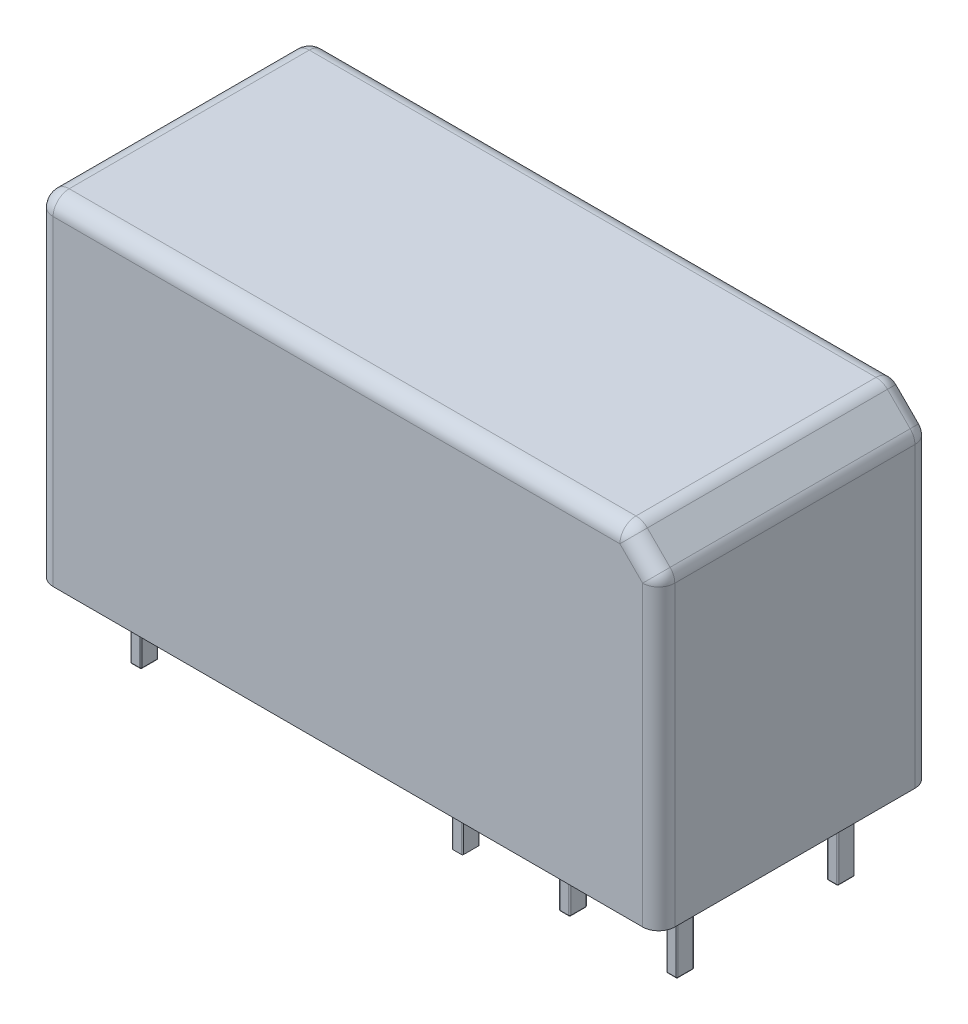
SolidWorks part; units mm, degrees
ref_plane "Спереди" through (0, 0, 0) normal (0, 0, 1) x (1, 0, 0)
ref_plane "Сверху" through (0, 0, 0) normal (0, 1, 0) x (1, 0, 0)
ref_plane "Справа" through (0, 0, 0) normal (1, 0, 0) x (0, 0, -1)
sketch "Эскиз1" plane through (0, 0, 0) normal (0, 1, 0) x (1, 0, 0)
  line L1 (-14.5, -6.35) -> (14.5, -6.35)
  line L2 (-14.5, -6.35) -> (-14.5, 6.35)
  line L3 (-14.5, 6.35) -> (14.5, 6.35)
  line L4 (14.5, -6.35) -> (14.5, 6.35)
  line L5 (-14.5, -6.35) -> (14.5, 6.35) construction
  line L6 (-14.5, 6.35) -> (14.5, -6.35) construction
  point P0 (0, 0)
  dimension "D1" = 29
  dimension "D2" = 12.7
extrude "Бобышка-Вытянуть1" add sketch "Эскиз1" along normal blind 15.7
sketch "Эскиз2" plane through (0, 0, 0) normal (0, -1, 0) x (1, 0, 0)
  line L0 (-14.5, -6.35) -> (-14.5, 6.35) construction
  line L1 (-12.3, 4.15) -> (-11.9, 4.15)
  line L2 (-12.35, 4.1) -> (-12.35, 3.4)
  line L3 (-12.3, 3.35) -> (-11.9, 3.35)
  line L4 (-11.85, 4.1) -> (-11.85, 3.4)
  line L5 (-12.35, 4.15) -> (-11.85, 3.35) construction
  line L6 (-12.35, 3.35) -> (-11.85, 4.15) construction
  line L7 (-7.35, 4.1) -> (-7.35, 3.4) [skipped]
  line L8 (-6.85, 4.1) -> (-6.85, 3.4) [skipped]
  line L9 (-7.3, 4.15) -> (-6.9, 4.15) [skipped]
  line L10 (-7.3, 3.35) -> (-6.9, 3.35) [skipped]
  line L11 (-2.35, 4.1) -> (-2.35, 3.4) [skipped]
  line L12 (-1.85, 4.1) -> (-1.85, 3.4) [skipped]
  line L13 (-2.3, 4.15) -> (-1.9, 4.15) [skipped]
  line L14 (-2.3, 3.35) -> (-1.9, 3.35) [skipped]
  line L15 (2.65, 4.1) -> (2.65, 3.4)
  line L16 (3.15, 4.1) -> (3.15, 3.4)
  line L17 (2.7, 4.15) -> (3.1, 4.15)
  line L18 (2.7, 3.35) -> (3.1, 3.35)
  line L19 (7.65, 4.1) -> (7.65, 3.4)
  line L20 (8.15, 4.1) -> (8.15, 3.4)
  line L21 (7.7, 4.15) -> (8.1, 4.15)
  line L22 (7.7, 3.35) -> (8.1, 3.35)
  line L23 (12.65, 4.1) -> (12.65, 3.4)
  line L24 (13.15, 4.1) -> (13.15, 3.4)
  line L25 (12.7, 4.15) -> (13.1, 4.15)
  line L26 (12.7, 3.35) -> (13.1, 3.35)
  line L27 (-7.35, -3.4) -> (-7.35, -4.1) [skipped]
  line L28 (-6.85, -3.4) -> (-6.85, -4.1) [skipped]
  line L29 (-7.3, -3.35) -> (-6.9, -3.35) [skipped]
  line L30 (-7.3, -4.15) -> (-6.9, -4.15) [skipped]
  line L31 (-2.35, -3.4) -> (-2.35, -4.1) [skipped]
  line L32 (-1.85, -3.4) -> (-1.85, -4.1) [skipped]
  line L33 (-2.3, -3.35) -> (-1.9, -3.35) [skipped]
  line L34 (-2.3, -4.15) -> (-1.9, -4.15) [skipped]
  line L35 (2.65, -3.4) -> (2.65, -4.1)
  line L36 (3.15, -3.4) -> (3.15, -4.1)
  line L37 (2.7, -3.35) -> (3.1, -3.35)
  line L38 (2.7, -4.15) -> (3.1, -4.15)
  line L39 (7.65, -3.4) -> (7.65, -4.1)
  line L40 (8.15, -3.4) -> (8.15, -4.1)
  line L41 (7.7, -3.35) -> (8.1, -3.35)
  line L42 (7.7, -4.15) -> (8.1, -4.15)
  line L43 (12.65, -3.4) -> (12.65, -4.1)
  line L44 (13.15, -3.4) -> (13.15, -4.1)
  line L45 (12.7, -3.35) -> (13.1, -3.35)
  line L46 (12.7, -4.15) -> (13.1, -4.15)
  line L47 (-12.35, -3.4) -> (-12.35, -4.1)
  line L48 (-11.85, -3.4) -> (-11.85, -4.1)
  line L49 (-12.3, -3.35) -> (-11.9, -3.35)
  line L50 (-12.3, -4.15) -> (-11.9, -4.15)
  arc A0 (-12.35, 3.4) -> (-12.3, 3.35) centre (-12.3, 3.4) ccw
  arc A1 (-11.9, 3.35) -> (-11.85, 3.4) centre (-11.9, 3.4) ccw
  arc A2 (-11.9, 4.15) -> (-11.85, 4.1) centre (-11.9, 4.1) cw
  arc A3 (-12.3, 4.15) -> (-12.35, 4.1) centre (-12.3, 4.1) ccw
  arc A4 (-7.35, 3.4) -> (-7.3, 3.35) centre (-7.3, 3.4) ccw [skipped]
  arc A5 (-6.9, 3.35) -> (-6.85, 3.4) centre (-6.9, 3.4) ccw [skipped]
  arc A6 (-6.9, 4.15) -> (-6.85, 4.1) centre (-6.9, 4.1) cw [skipped]
  arc A7 (-7.3, 4.15) -> (-7.35, 4.1) centre (-7.3, 4.1) ccw [skipped]
  arc A8 (-2.35, 3.4) -> (-2.3, 3.35) centre (-2.3, 3.4) ccw [skipped]
  arc A9 (-1.9, 3.35) -> (-1.85, 3.4) centre (-1.9, 3.4) ccw [skipped]
  arc A10 (-1.9, 4.15) -> (-1.85, 4.1) centre (-1.9, 4.1) cw [skipped]
  arc A11 (-2.3, 4.15) -> (-2.35, 4.1) centre (-2.3, 4.1) ccw [skipped]
  arc A12 (2.65, 3.4) -> (2.7, 3.35) centre (2.7, 3.4) ccw
  arc A13 (3.1, 3.35) -> (3.15, 3.4) centre (3.1, 3.4) ccw
  arc A14 (3.1, 4.15) -> (3.15, 4.1) centre (3.1, 4.1) cw
  arc A15 (2.7, 4.15) -> (2.65, 4.1) centre (2.7, 4.1) ccw
  arc A16 (7.65, 3.4) -> (7.7, 3.35) centre (7.7, 3.4) ccw
  arc A17 (8.1, 3.35) -> (8.15, 3.4) centre (8.1, 3.4) ccw
  arc A18 (8.1, 4.15) -> (8.15, 4.1) centre (8.1, 4.1) cw
  arc A19 (7.7, 4.15) -> (7.65, 4.1) centre (7.7, 4.1) ccw
  arc A20 (12.65, 3.4) -> (12.7, 3.35) centre (12.7, 3.4) ccw
  arc A21 (13.1, 3.35) -> (13.15, 3.4) centre (13.1, 3.4) ccw
  arc A22 (13.1, 4.15) -> (13.15, 4.1) centre (13.1, 4.1) cw
  arc A23 (12.7, 4.15) -> (12.65, 4.1) centre (12.7, 4.1) ccw
  arc A24 (-7.35, -4.1) -> (-7.3, -4.15) centre (-7.3, -4.1) ccw [skipped]
  arc A25 (-6.9, -4.15) -> (-6.85, -4.1) centre (-6.9, -4.1) ccw [skipped]
  arc A26 (-6.9, -3.35) -> (-6.85, -3.4) centre (-6.9, -3.4) cw [skipped]
  arc A27 (-7.3, -3.35) -> (-7.35, -3.4) centre (-7.3, -3.4) ccw [skipped]
  arc A28 (-2.35, -4.1) -> (-2.3, -4.15) centre (-2.3, -4.1) ccw [skipped]
  arc A29 (-1.9, -4.15) -> (-1.85, -4.1) centre (-1.9, -4.1) ccw [skipped]
  arc A30 (-1.9, -3.35) -> (-1.85, -3.4) centre (-1.9, -3.4) cw [skipped]
  arc A31 (-2.3, -3.35) -> (-2.35, -3.4) centre (-2.3, -3.4) ccw [skipped]
  arc A32 (2.65, -4.1) -> (2.7, -4.15) centre (2.7, -4.1) ccw
  arc A33 (3.1, -4.15) -> (3.15, -4.1) centre (3.1, -4.1) ccw
  arc A34 (3.1, -3.35) -> (3.15, -3.4) centre (3.1, -3.4) cw
  arc A35 (2.7, -3.35) -> (2.65, -3.4) centre (2.7, -3.4) ccw
  arc A36 (7.65, -4.1) -> (7.7, -4.15) centre (7.7, -4.1) ccw
  arc A37 (8.1, -4.15) -> (8.15, -4.1) centre (8.1, -4.1) ccw
  arc A38 (8.1, -3.35) -> (8.15, -3.4) centre (8.1, -3.4) cw
  arc A39 (7.7, -3.35) -> (7.65, -3.4) centre (7.7, -3.4) ccw
  arc A40 (12.65, -4.1) -> (12.7, -4.15) centre (12.7, -4.1) ccw
  arc A41 (13.1, -4.15) -> (13.15, -4.1) centre (13.1, -4.1) ccw
  arc A42 (13.1, -3.35) -> (13.15, -3.4) centre (13.1, -3.4) cw
  arc A43 (12.7, -3.35) -> (12.65, -3.4) centre (12.7, -3.4) ccw
  arc A44 (-12.35, -4.1) -> (-12.3, -4.15) centre (-12.3, -4.1) ccw
  arc A45 (-11.9, -4.15) -> (-11.85, -4.1) centre (-11.9, -4.1) ccw
  arc A46 (-11.9, -3.35) -> (-11.85, -3.4) centre (-11.9, -3.4) cw
  arc A47 (-12.3, -3.35) -> (-12.35, -3.4) centre (-12.3, -3.4) ccw
  point P0 (-12.1, 3.75)
  point P8 (-14.5, 0)
  point P21 (-11.85, 3.75)
  dimension "D1" = 0.05
  dimension "D2" = 0.5
  dimension "D3" = 3.75
  dimension "D4" = 2.4
  dimension "D5" = 0.8
  dimension "D6" = 6
  dimension "D7" = 2
extrude "Бобышка-Вытянуть2" add sketch "Эскиз2" along normal blind 3.5
fillet "Скругление1" radius 0.05 48 edges at (-11.8646, -3.5, 3.3646) (-12.1, -3.5, 3.35) (-12.3354, -3.5, 3.3646) (-12.35, -3.5, 3.75) (-12.3354, -3.5, 4.1354) (-12.1, -3.5, 4.15) (-11.8646, -3.5, 4.1354) (-11.8646, -3.5, -4.1354) (-12.1, -3.5, -4.15) (-12.3354, -3.5, -4.1354) (-12.35, -3.5, -3.75) (-12.3354, -3.5, -3.3646) (-12.1, -3.5, -3.35) (-11.8646, -3.5, -3.3646) (13.1354, -3.5, 3.3646) (12.9, -3.5, 3.35) (12.6646, -3.5, 3.3646) (12.65, -3.5, 3.75) (12.6646, -3.5, 4.1354) (12.9, -3.5, 4.15) (13.1354, -3.5, 4.1354) (8.1354, -3.5, 3.3646) (7.9, -3.5, 3.35) (7.6646, -3.5, 3.3646) (7.65, -3.5, 3.75) (7.6646, -3.5, 4.1354) (7.9, -3.5, 4.15) (8.1354, -3.5, 4.1354) (8.1354, -3.5, -4.1354) (7.9, -3.5, -4.15) (7.6646, -3.5, -4.1354) (7.65, -3.5, -3.75) (7.6646, -3.5, -3.3646) (7.9, -3.5, -3.35) (8.1354, -3.5, -3.3646) (13.1354, -3.5, -4.1354) (12.9, -3.5, -4.15) (12.6646, -3.5, -4.1354) (12.65, -3.5, -3.75) (12.6646, -3.5, -3.3646) (12.9, -3.5, -3.35) (13.1354, -3.5, -3.3646) (-11.85, -3.5, 3.75) (-11.85, -3.5, -3.75) (13.15, -3.5, 3.75) (8.15, -3.5, 3.75) (8.15, -3.5, -3.75) (13.15, -3.5, -3.75)
chamfer "Фаска1" distance 1.5 angle 45 1 edges at (14.5, 15.7, 0)
fillet "Скругление2" radius 0.75 11 edges at (13.75, 14.95, -6.35) (-14.5, 7.85, 6.35) (-14.5, 7.85, -6.35) (14.5, 7.1, -6.35) (14.5, 7.1, 6.35) (13.75, 14.95, 6.35) (14.5, 14.2, 0) (13, 15.7, 0) (-0.75, 15.7, -6.35) (-14.5, 15.7, 0) (-0.75, 15.7, 6.35)
